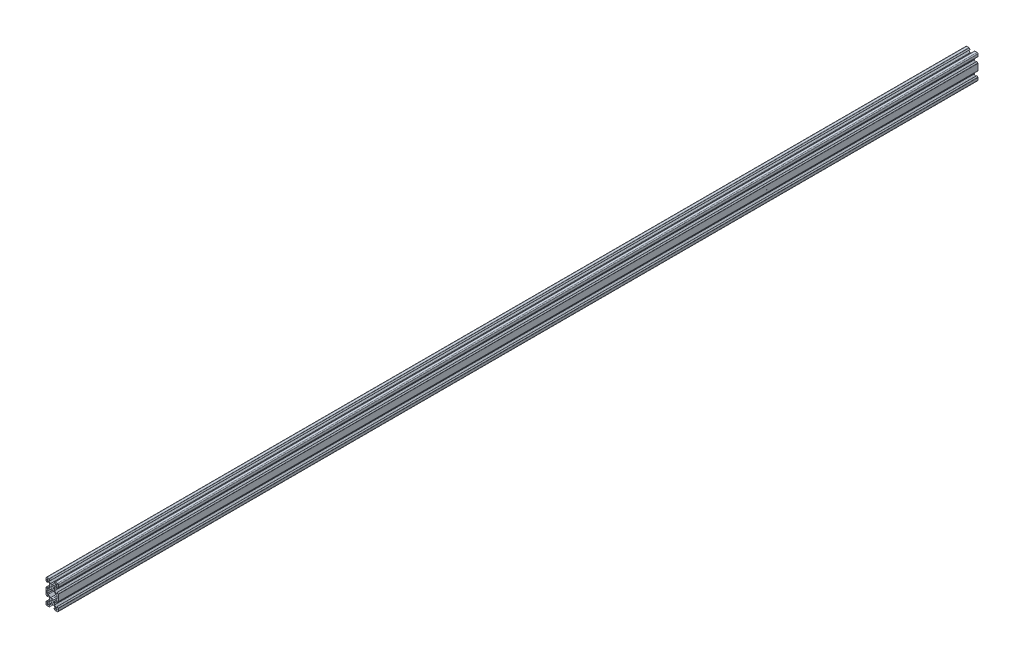
SolidWorks part; units mm, degrees
ref_plane "Front Plane" through (0, 0, 0) normal (0, 0, 1) x (1, 0, 0)
ref_plane "Top Plane" through (0, 0, 0) normal (0, 1, 0) x (1, 0, 0)
ref_plane "Right Plane" through (0, 0, 0) normal (1, 0, 0) x (0, 0, -1)
sketch "Sketch1" plane through (0, 0, 0) normal (0, 0, 1) x (1, 0, 0)
  line L0 (-8.2, 2.8875) -> (-8.2, 5.4975)
  line L3 (-4.9072, 9.9975) -> (-8.5, 9.9975)
  line L4 (-10, 4.9047) -> (-10, 8.4975)
  line L5 (-2.1, 0) -> (-3.8, 0) construction
  line L6 (0, 3.8) -> (0, 0) construction
  line L7 (-0.1, 3.9) -> (-2.8404, 3.9)
  line L8 (-3.9, 0.1) -> (-3.9, 2.8383)
  line L9 (-2.89, 8.1975) -> (-5.5, 8.1975)
  line L10 (-6.57, 8.1975) -> (-6.57, 7.6575)
  line L11 (-8.2, 6.5675) -> (-7.66, 6.5675)
  line L12 (-5.5, 8.1975) -> (-5.5, 6.5588)
  line L13 (-6.56, 5.4975) -> (-8.2, 5.4975)
  line L14 (-8.2, 8.1975) -> (-1.4852, 1.4847) construction
  line L15 (-6.56, 5.4975) -> (-3.9, 2.8383)
  line L16 (-5.5, 6.5588) -> (-2.8404, 3.9)
  line L17 (-7.66, 6.5675) -> (-6.57, 7.6575)
  line L18 (-8.7302, 7.6671) -> (-0.5302, -0.5304) construction
  line L19 (-7.6698, 8.7279) -> (0.5302, 0.5304) construction
  line L20 (-8.2, 8.1975) -> (0, 0) construction
  line L21 (-8.2, 6.5675) -> (-8.2, 8.1975)
  line L22 (-8.2, -0.0025) -> (-8.2, 8.1975) construction
  line L23 (-6.57, 8.1975) -> (-8.2, 8.1975)
  line L24 (0, 8.1975) -> (-8.2, 8.1975) construction
  line L25 (-10, -0.0025) -> (-10, 9.9975) construction
  line L26 (0, 9.9975) -> (-10, 9.9975) construction
  line L27 (-2.89, 8.3075) -> (-2.89, 8.1975)
  line L29 (-8.31, 2.8875) -> (-8.2, 2.8875)
  line L30 (-4.3486, 9.7661) -> (-2.89, 8.3075)
  line L31 (-8.31, 2.8875) -> (-9.7686, 4.3461)
  line L34 (-0.1, 3.9) -> (0, 3.8)
  line L35 (-3.9, 0.1) -> (-3.8, 0)
  line L36 (-8.2, -7.2996) -> (-6.24, -7.2996)
  line L37 (0, 0) -> (0, -10) construction
  line L38 (-0.1, -3.9) -> (-2.8404, -3.9)
  line L39 (-3.8, 0) -> (-3.9, -0.1)
  line L40 (-3.9, -0.1) -> (-3.9, -2.84)
  line L41 (-2.8404, -3.9) -> (-6.24, -7.2996)
  line L42 (-3.9, -2.84) -> (-6.56, -5.5)
  line L43 (-8.2, -2.89) -> (-8.2, -5.5)
  line L44 (-6.56, 5.4975) -> (-6.56, -5.5) construction
  line L45 (-6.56, -5.5) -> (-8.2, -5.5)
  line L46 (-0.1, -3.9) -> (0, -3.8)
  line L48 (-8.2, -2.89) -> (-8.31, -2.89)
  line L49 (-8.31, -2.89) -> (-9.7657, -4.3457)
  line L52 (-10, -10) -> (0, -10) construction
  line L53 (-8.2, -7.2996) -> (-8.2, -10)
  line L61 (-10, -4.9114) -> (-10, -10)
  arc A1 (-10, 8.4975) -> (-8.5, 9.9975) centre (-8.5, 8.4975) cw
  arc A2 (-9.7686, 4.3461) -> (-10, 4.9047) centre (-9.21, 4.9047) cw
  arc A3 (-4.3486, 9.7661) -> (-4.9072, 9.9975) centre (-4.9072, 9.2075) ccw
  arc A4 (-9.7657, -4.3457) -> (-10, -4.9114) centre (-9.2, -4.9114) ccw
  arc A6 (0, 2.1) -> (0, -2.1) centre (0, 0) ccw
  point P29 (-10, 9.9975)
  point P39 (-10, 4.5775)
  point P42 (-4.58, 9.9975)
  point P48 (-10, -4.58)
  dimension "D15" = 1.5
  dimension "D22" = 0.79
  dimension "D30" = 1.96
  dimension "D31" = 2.1
  dimension "D39" = 0.8
  dimension "D4" = 1.8
  dimension "D5" = 3.43
  dimension "D6" = 3.43
  dimension "D7" = 0.54
  dimension "D8" = 0.54
  dimension "D9" = 1.07
  dimension "D10" = 1.07
  dimension "D11" = 3.9
  dimension "D12" = 3.9
  dimension "D16" = 7.11
  dimension "D17" = 0.11
  dimension "D18" = 1.69
  dimension "D19" = 0.11
  dimension "D20" = 7.11
  dimension "D21" = 1.69
  dimension "D23" = 10
  dimension "D24" = 0.1
  dimension "D25" = 45
  dimension "D26" = 0.1
  dimension "D27" = 45
  dimension "D28" = 1.64
  dimension "D29" = 10
  dimension "D32" = 3.9
  dimension "D33" = 45
  dimension "D34" = 2.74
  dimension "D35" = 45
  dimension "D37" = 2.61
  dimension "D38" = 90
  dimension "D40" = 0.1
  dimension "D41" = 45
  dimension "D13" = 0.75
  dimension "D14" = 0.75
sketch "Sketch2" plane through (0, 0, 0) normal (0, 0, 1) x (1, 0, 0)
  line L0 (-0.1, 3.9) -> (0, 3.8) construction
  line L1 (-0.1, 3.9) -> (-2.8404, 3.9) construction
  line L2 (-5.5, 6.5588) -> (-2.8404, 3.9) construction
  line L3 (-5.5, 8.1975) -> (-5.5, 6.5588) construction
  line L4 (-2.89, 8.1975) -> (-5.5, 8.1975) construction
  line L5 (-7.66, 6.5675) -> (-6.57, 7.6575)
  line L6 (-6.57, 7.6575) -> (-6.57, 8.1975)
  line L7 (-6.57, 8.1975) -> (-8.2, 8.1975)
  line L8 (-8.2, 8.1975) -> (-8.2, 6.5675)
  line L9 (-8.2, 6.5675) -> (-7.66, 6.5675)
  line L10 (-7.66, 6.5675) -> (-6.57, 7.6575)
  line L11 (-6.57, 7.6575) -> (-6.57, 8.1975)
  line L12 (-6.57, 8.1975) -> (-8.2, 8.1975)
  line L13 (-8.2, 8.1975) -> (-8.2, 6.5675)
  line L14 (-8.2, 6.5675) -> (-7.66, 6.5675)
  line L15 (-2.89, 8.3075) -> (-2.89, 8.1975) construction
  line L16 (-4.3486, 9.7661) -> (-2.89, 8.3075) construction
  line L17 (-4.9072, 9.9975) -> (-8.5, 9.9975) construction
  line L18 (-10, 4.9047) -> (-10, 8.4975) construction
  line L19 (-8.31, 2.8875) -> (-9.7686, 4.3461) construction
  line L20 (-8.31, 2.8875) -> (-8.2, 2.8875) construction
  line L21 (-8.2, 2.8875) -> (-8.2, 5.4975) construction
  line L22 (-6.56, 5.4975) -> (-8.2, 5.4975) construction
  line L23 (-6.56, 5.4975) -> (-3.9, 2.8383) construction
  line L24 (-3.9, 0.1) -> (-3.9, 2.8383) construction
  line L25 (-3.9, 0.1) -> (-3.8, 0) construction
  line L26 (-3.8, 0) -> (-3.9, -0.1) construction
  line L27 (-3.9, -0.1) -> (-3.9, -2.84) construction
  line L28 (-3.9, -2.84) -> (-6.56, -5.5) construction
  line L29 (-6.56, -5.5) -> (-8.2, -5.5) construction
  line L30 (-8.2, -2.89) -> (-8.2, -5.5) construction
  line L31 (-8.2, -2.89) -> (-8.31, -2.89) construction
  line L32 (-8.31, -2.89) -> (-9.7657, -4.3457) construction
  line L33 (-10, -4.9114) -> (-10, -10) construction
  line L34 (-0.1, -3.9) -> (0, -3.8) construction
  line L35 (-0.1, -3.9) -> (-2.8404, -3.9) construction
  line L36 (-2.8404, -3.9) -> (-6.24, -7.2996) construction
  line L37 (-8.2, -7.2996) -> (-6.24, -7.2996) construction
  line L38 (-8.2, -7.2996) -> (-8.2, -10) construction
  line L39 (-0.1, 3.9) -> (0, 3.8)
  line L40 (-0.1, 3.9) -> (-2.8404, 3.9)
  line L41 (-5.5, 6.5588) -> (-2.8404, 3.9)
  line L42 (-5.5, 8.1975) -> (-5.5, 6.5588)
  line L43 (-2.89, 8.1975) -> (-5.5, 8.1975)
  line L44 (-2.89, 8.3075) -> (-2.89, 8.1975)
  line L45 (-4.3486, 9.7661) -> (-2.89, 8.3075)
  line L46 (-4.9072, 9.9975) -> (-8.5, 9.9975)
  line L47 (-10, 4.9047) -> (-10, 8.4975)
  line L48 (-8.31, 2.8875) -> (-9.7686, 4.3461)
  line L49 (-8.31, 2.8875) -> (-8.2, 2.8875)
  line L50 (-8.2, 2.8875) -> (-8.2, 5.4975)
  line L51 (-6.56, 5.4975) -> (-8.2, 5.4975)
  line L52 (-6.56, 5.4975) -> (-3.9, 2.8383)
  line L53 (-3.9, 0.1) -> (-3.9, 2.8383)
  line L54 (-3.9, 0.1) -> (-3.8, 0)
  line L55 (-3.8, 0) -> (-3.9, -0.1)
  line L56 (-3.9, -0.1) -> (-3.9, -2.84)
  line L57 (-3.9, -2.84) -> (-6.56, -5.5)
  line L58 (-6.56, -5.5) -> (-8.2, -5.5)
  line L59 (-8.2, -2.89) -> (-8.2, -5.5)
  line L60 (-8.2, -2.89) -> (-8.31, -2.89)
  line L61 (-8.31, -2.89) -> (-9.7657, -4.3457)
  line L62 (-10, -4.9114) -> (-10, -15.0886)
  line L63 (-0.1, -3.9) -> (0, -3.8)
  line L64 (-0.1, -3.9) -> (-2.8404, -3.9)
  line L65 (-2.8404, -3.9) -> (-6.24, -7.2996)
  line L66 (-8.2, -7.2996) -> (-6.24, -7.2996)
  line L67 (-8.2, -7.2996) -> (-8.2, -12.7004)
  line L68 (0, 0) -> (0, -10) construction
  line L69 (-10, -10) -> (0, -10) construction
  line L70 (0, 0) -> (0, -20) construction
  line L71 (-10, -10) -> (10, -10) construction
  line L72 (8.2, -7.2996) -> (8.2, -12.7004)
  line L73 (8.2, -7.2996) -> (6.24, -7.2996)
  line L74 (2.8404, -3.9) -> (6.24, -7.2996)
  line L75 (0.1, -3.9) -> (2.8404, -3.9)
  line L76 (0.1, -3.9) -> (0, -3.8)
  line L77 (10, -4.9114) -> (10, -15.0886)
  line L78 (8.31, -2.89) -> (9.7657, -4.3457)
  line L79 (8.2, -2.89) -> (8.31, -2.89)
  line L80 (8.2, -2.89) -> (8.2, -5.5)
  line L81 (6.56, -5.5) -> (8.2, -5.5)
  line L82 (3.9, -2.84) -> (6.56, -5.5)
  line L83 (3.9, -0.1) -> (3.9, -2.84)
  line L84 (3.8, 0) -> (3.9, -0.1)
  line L85 (3.9, 0.1) -> (3.8, 0)
  line L86 (3.9, 0.1) -> (3.9, 2.8383)
  line L87 (6.56, 5.4975) -> (3.9, 2.8383)
  line L88 (6.56, 5.4975) -> (8.2, 5.4975)
  line L89 (8.2, 2.8875) -> (8.2, 5.4975)
  line L90 (8.31, 2.8875) -> (8.2, 2.8875)
  line L91 (8.31, 2.8875) -> (9.7686, 4.3461)
  line L92 (10, 4.9047) -> (10, 8.4975)
  line L93 (4.9072, 9.9975) -> (8.5, 9.9975)
  line L94 (4.3486, 9.7661) -> (2.89, 8.3075)
  line L95 (2.89, 8.3075) -> (2.89, 8.1975)
  line L96 (2.89, 8.1975) -> (5.5, 8.1975)
  line L97 (5.5, 8.1975) -> (5.5, 6.5588)
  line L98 (5.5, 6.5588) -> (2.8404, 3.9)
  line L99 (0.1, 3.9) -> (2.8404, 3.9)
  line L100 (0.1, 3.9) -> (0, 3.8)
  line L101 (8.2, 6.5675) -> (7.66, 6.5675)
  line L102 (8.2, 8.1975) -> (8.2, 6.5675)
  line L103 (6.57, 8.1975) -> (8.2, 8.1975)
  line L104 (6.57, 7.6575) -> (6.57, 8.1975)
  line L105 (7.66, 6.5675) -> (6.57, 7.6575)
  line L106 (7.66, -26.5675) -> (6.57, -27.6575)
  line L107 (6.57, -27.6575) -> (6.57, -28.1975)
  line L108 (6.57, -28.1975) -> (8.2, -28.1975)
  line L109 (8.2, -28.1975) -> (8.2, -26.5675)
  line L110 (8.2, -26.5675) -> (7.66, -26.5675)
  line L111 (0.1, -23.9) -> (0, -23.8)
  line L112 (0.1, -23.9) -> (2.8404, -23.9)
  line L113 (5.5, -26.5588) -> (2.8404, -23.9)
  line L114 (5.5, -28.1975) -> (5.5, -26.5588)
  line L115 (2.89, -28.1975) -> (5.5, -28.1975)
  line L116 (2.89, -28.3075) -> (2.89, -28.1975)
  line L117 (4.3486, -29.7661) -> (2.89, -28.3075)
  line L118 (4.9072, -29.9975) -> (8.5, -29.9975)
  line L119 (10, -24.9047) -> (10, -28.4975)
  line L120 (8.31, -22.8875) -> (9.7686, -24.3461)
  line L121 (8.31, -22.8875) -> (8.2, -22.8875)
  line L122 (8.2, -22.8875) -> (8.2, -25.4975)
  line L123 (6.56, -25.4975) -> (8.2, -25.4975)
  line L124 (6.56, -25.4975) -> (3.9, -22.8383)
  line L125 (3.9, -20.1) -> (3.9, -22.8383)
  line L126 (3.9, -20.1) -> (3.8, -20)
  line L127 (3.8, -20) -> (3.9, -19.9)
  line L128 (3.9, -19.9) -> (3.9, -17.16)
  line L129 (3.9, -17.16) -> (6.56, -14.5)
  line L130 (6.56, -14.5) -> (8.2, -14.5)
  line L131 (8.2, -17.11) -> (8.2, -14.5)
  line L132 (8.2, -17.11) -> (8.31, -17.11)
  line L133 (8.31, -17.11) -> (9.7657, -15.6543)
  line L134 (0.1, -16.1) -> (0, -16.2)
  line L135 (0.1, -16.1) -> (2.8404, -16.1)
  line L136 (2.8404, -16.1) -> (6.24, -12.7004)
  line L137 (8.2, -12.7004) -> (6.24, -12.7004)
  line L138 (-8.2, -12.7004) -> (-6.24, -12.7004)
  line L139 (-2.8404, -16.1) -> (-6.24, -12.7004)
  line L140 (-0.1, -16.1) -> (-2.8404, -16.1)
  line L141 (-0.1, -16.1) -> (0, -16.2)
  line L142 (-8.31, -17.11) -> (-9.7657, -15.6543)
  line L143 (-8.2, -17.11) -> (-8.31, -17.11)
  line L144 (-8.2, -17.11) -> (-8.2, -14.5)
  line L145 (-6.56, -14.5) -> (-8.2, -14.5)
  line L146 (-3.9, -17.16) -> (-6.56, -14.5)
  line L147 (-3.9, -19.9) -> (-3.9, -17.16)
  line L148 (-3.8, -20) -> (-3.9, -19.9)
  line L149 (-3.9, -20.1) -> (-3.8, -20)
  line L150 (-3.9, -20.1) -> (-3.9, -22.8383)
  line L151 (-6.56, -25.4975) -> (-3.9, -22.8383)
  line L152 (-6.56, -25.4975) -> (-8.2, -25.4975)
  line L153 (-8.2, -22.8875) -> (-8.2, -25.4975)
  line L154 (-8.31, -22.8875) -> (-8.2, -22.8875)
  line L155 (-8.31, -22.8875) -> (-9.7686, -24.3461)
  line L156 (-10, -24.9047) -> (-10, -28.4975)
  line L157 (-4.9072, -29.9975) -> (-8.5, -29.9975)
  line L158 (-4.3486, -29.7661) -> (-2.89, -28.3075)
  line L159 (-2.89, -28.3075) -> (-2.89, -28.1975)
  line L160 (-2.89, -28.1975) -> (-5.5, -28.1975)
  line L161 (-5.5, -28.1975) -> (-5.5, -26.5588)
  line L162 (-5.5, -26.5588) -> (-2.8404, -23.9)
  line L163 (-0.1, -23.9) -> (-2.8404, -23.9)
  line L164 (-0.1, -23.9) -> (0, -23.8)
  line L165 (-8.2, -26.5675) -> (-7.66, -26.5675)
  line L166 (-8.2, -28.1975) -> (-8.2, -26.5675)
  line L167 (-6.57, -28.1975) -> (-8.2, -28.1975)
  line L168 (-6.57, -27.6575) -> (-6.57, -28.1975)
  line L169 (-7.66, -26.5675) -> (-6.57, -27.6575)
  arc A0 (0, 2.1) -> (0, -2.1) centre (0, 0) ccw construction
  arc A1 (-4.3486, 9.7661) -> (-4.9072, 9.9975) centre (-4.9072, 9.2075) ccw construction
  arc A2 (-8.5, 9.9975) -> (-10, 8.4975) centre (-8.5, 8.4975) ccw construction
  arc A3 (-10, 4.9047) -> (-9.7686, 4.3461) centre (-9.21, 4.9047) ccw construction
  arc A4 (-9.7657, -4.3457) -> (-10, -4.9114) centre (-9.2, -4.9114) ccw construction
  circle A5 centre (0, 0) radius 2.1
  arc A6 (-4.3486, 9.7661) -> (-4.9072, 9.9975) centre (-4.9072, 9.2075) ccw
  arc A7 (-8.5, 9.9975) -> (-10, 8.4975) centre (-8.5, 8.4975) ccw
  arc A8 (-10, 4.9047) -> (-9.7686, 4.3461) centre (-9.21, 4.9047) ccw
  arc A9 (-9.7657, -4.3457) -> (-10, -4.9114) centre (-9.2, -4.9114) ccw
  arc A10 (9.7657, -4.3457) -> (10, -4.9114) centre (9.2, -4.9114) cw
  arc A11 (10, 4.9047) -> (9.7686, 4.3461) centre (9.21, 4.9047) cw
  arc A12 (8.5, 9.9975) -> (10, 8.4975) centre (8.5, 8.4975) cw
  arc A13 (4.3486, 9.7661) -> (4.9072, 9.9975) centre (4.9072, 9.2075) cw
  arc A14 (4.3486, -29.7661) -> (4.9072, -29.9975) centre (4.9072, -29.2075) ccw
  arc A15 (8.5, -29.9975) -> (10, -28.4975) centre (8.5, -28.4975) ccw
  arc A16 (10, -24.9047) -> (9.7686, -24.3461) centre (9.21, -24.9047) ccw
  arc A17 (9.7657, -15.6543) -> (10, -15.0886) centre (9.2, -15.0886) ccw
  arc A18 (-9.7657, -15.6543) -> (-10, -15.0886) centre (-9.2, -15.0886) cw
  arc A19 (-10, -24.9047) -> (-9.7686, -24.3461) centre (-9.21, -24.9047) cw
  arc A20 (-8.5, -29.9975) -> (-10, -28.4975) centre (-8.5, -28.4975) cw
  arc A21 (-4.3486, -29.7661) -> (-4.9072, -29.9975) centre (-4.9072, -29.2075) cw
  circle A22 centre (0, -20) radius 2.1
  point P147 (8.2, -10)
  dimension "D1" = 0
extrude "Boss-Extrude1" add sketch "Sketch2" against normal blind 1500
